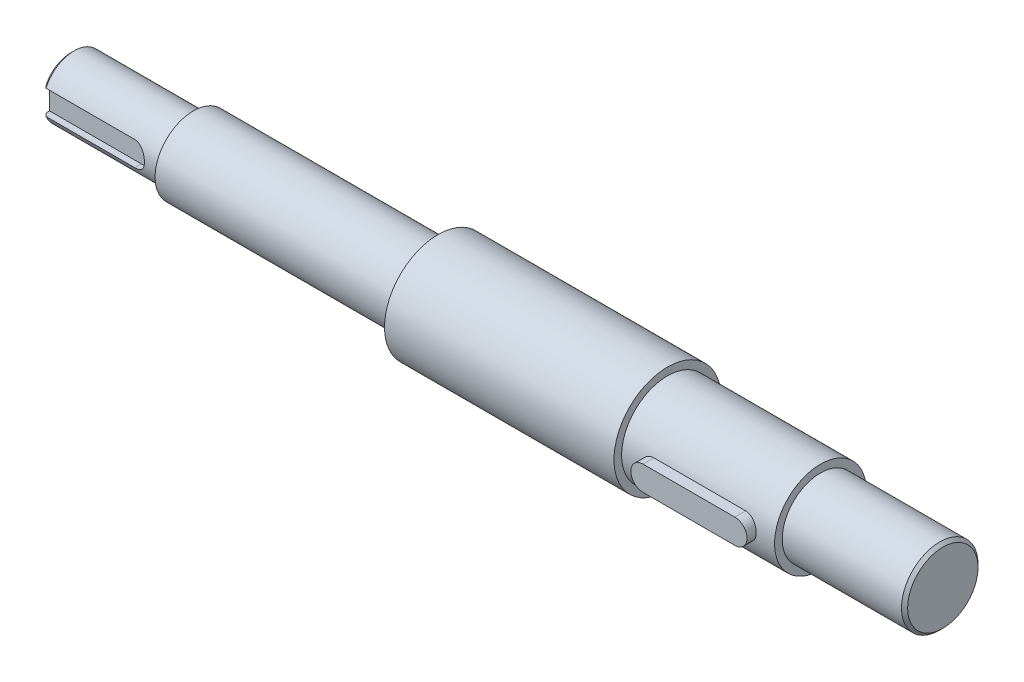
SolidWorks part; units mm, degrees
ref_plane "Front Plane" through (0, 0, 0) normal (0, 0, 1) x (1, 0, 0)
ref_plane "Top Plane" through (0, 0, 0) normal (0, 1, 0) x (1, 0, 0)
ref_plane "Right Plane" through (0, 0, 0) normal (1, 0, 0) x (0, 0, -1)
sketch "Sketch1" plane through (0, 0, 0) normal (0, 1, 0) x (1, 0, 0)
  line L0 (0, 0) -> (0, -10)
  line L1 (0, -10) -> (40, -10)
  line L2 (40, -10) -> (40, -12.5)
  line L3 (40, -12.5) -> (120, -12.5)
  line L4 (120, -12.5) -> (120, -17.5)
  line L5 (120, -17.5) -> (195, -17.5)
  line L6 (195, -17.5) -> (195, -15)
  line L7 (195, -15) -> (245, -15)
  line L8 (245, -15) -> (245, -12.5)
  line L9 (245, -12.5) -> (285, -12.5)
  line L10 (285, -12.5) -> (285, 0)
  line L11 (285, 0) -> (0, 0)
  dimension "D1" = 10
  dimension "D2" = 40
  dimension "D3" = 80
  dimension "D4" = 75
  dimension "D5" = 50
  dimension "D6" = 40
  dimension "D7" = 15
  dimension "D8" = 17.5
  dimension "D9" = 12.5
  dimension "D10" = 12.5
revolve "Revolve1" add sketch "Sketch1" angle 360 about L11
ref_plane "Plane1" through (0, 0, 15) normal (0, 0, -1) x (-1, 0, 0)
sketch "Sketch2" plane through (0, 0, 15) normal (0, 0, -1) x (-1, 0, 0)
  line L0 (0, 0) -> (-333.1724, 0) construction
  line L1 (-245, 15) -> (-245, -15) construction
  line L6 (-205, -4) -> (-235, -4)
  line L7 (-205, -4) -> (-205, 4)
  line L8 (-205, 4) -> (-235, 4)
  line L9 (-235, -4) -> (-235, 4)
  line L10 (-205, -4) -> (-235, 4) construction
  line L11 (-205, 4) -> (-235, -4) construction
  arc A1 (-235, 4) -> (-235, -4) centre (-235, 0) ccw
  arc A2 (-205, -4) -> (-205, 4) centre (-205, 0) ccw
  point P3 (-220, 0)
  dimension "D1" = 10
  dimension "D2" = 8
  dimension "D3" = 30
ref_plane "Plane2" through (0, 0, 10) normal (0, 0, 1) x (1, 0, 0)
sketch "Sketch3" plane through (0, 0, 10) normal (0, 0, 1) x (1, 0, 0)
  line L0 (0, 0) -> (-4.7873, 0) construction
  line L5 (0, 0) -> (333.1724, 0) construction
  line L6 (-12.75, -4) -> (30, -4)
  line L7 (-12.75, -4) -> (-12.75, 4)
  line L8 (-12.75, 4) -> (30, 4)
  line L9 (30, -4) -> (30, 4)
  line L10 (-12.75, -4) -> (30, 4) construction
  line L11 (-12.75, 4) -> (30, -4) construction
  line L12 (40, 10) -> (40, -10) construction
  arc A0 (30, -4) -> (30, 4) centre (30, 0) ccw
  point P0 (8.625, 0)
  dimension "D1" = 8
  dimension "D2" = 10
  dimension "D3" = 42.75
extrude "Cut-Extrude2" cut sketch "Sketch2" along normal blind 3 contours L9 L6 L7 L8 | L9 A1 | L7 A2
extrude "Cut-Extrude3" cut sketch "Sketch3" against normal blind 3 contours L6 L9 L8 L7 | L9 A0
chamfer "Chamfer1" distance 1 angle 45 2 edges at (285, 0, -12.5) (0, 0, -10)
ref_plane "Plane3" through (235, 4, 14.4568) normal (-1, 0, 0) x (0, 0, 1)
ref_plane "Plane4" through (235, -4, 14.4568) normal (-1, 0, 0) x (0, 0, 1)
sketch "Sketch9" plane through (0, 0, 12) normal (0, 0, 1) x (1, 0, 0)
  line L2 (235, 4) -> (205, 4)
  line L3 (205, -4) -> (235, -4)
  line L4 (235, 4) -> (205, 4)
  line L5 (205, -4) -> (235, -4)
  arc A2 (205, 4) -> (205, -4) centre (205, 0) ccw
  arc A3 (235, -4) -> (235, 4) centre (235, 0) ccw
  arc A4 (205, 4) -> (205, -4) centre (205, 0) ccw
  arc A5 (235, -4) -> (235, 4) centre (235, 0) ccw
  dimension "D1" = 0
extrude "Boss-Extrude1" add sketch "Sketch9" along normal blind 6
